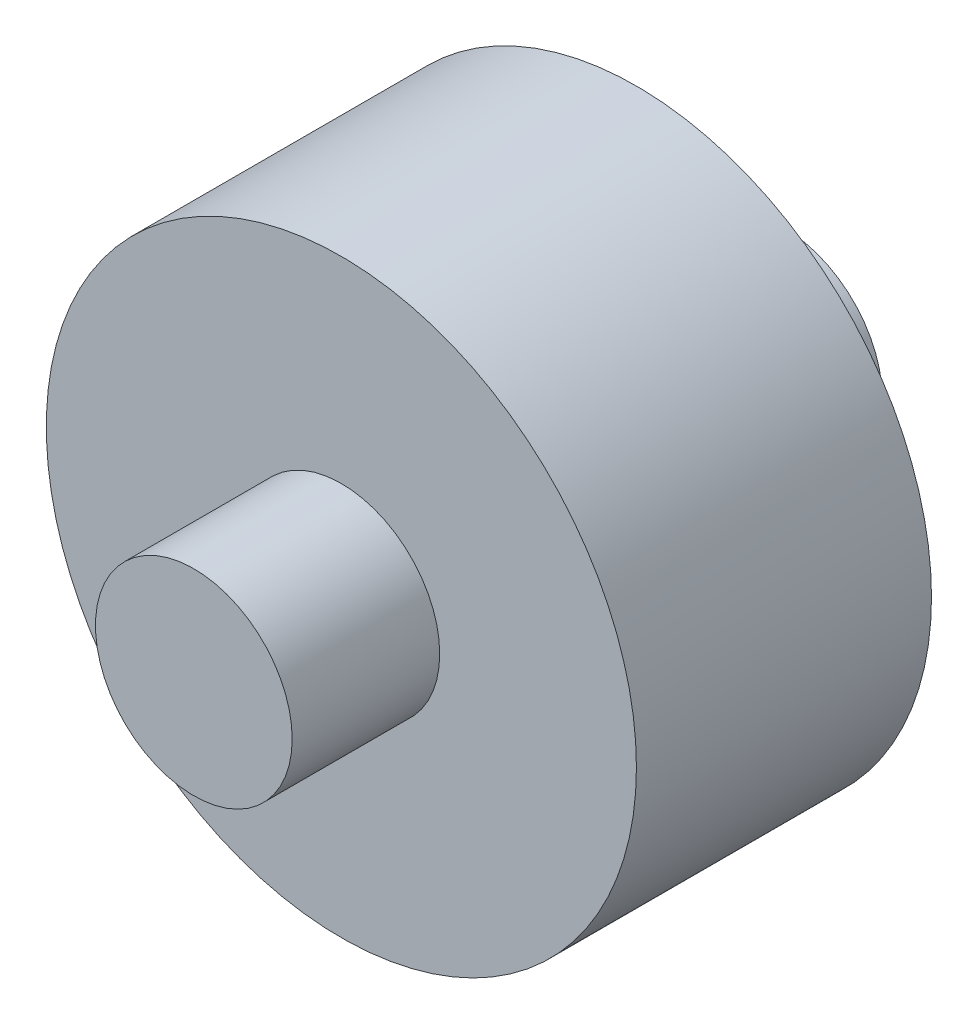
SolidWorks part; units mm, degrees
ref_plane "Front Plane" through (0, 0, 0) normal (0, 0, 1) x (1, 0, 0)
ref_plane "Top Plane" through (0, 0, 0) normal (0, 1, 0) x (1, 0, 0)
ref_plane "Right Plane" through (0, 0, 0) normal (1, 0, 0) x (0, 0, -1)
sketch "Sketch1" plane through (0, 0, 0) normal (0, 0, 1) x (1, 0, 0)
  circle A0 centre (0, 0) radius 9.525
  dimension "D1" = 19.05
extrude "Boss-Extrude1" add sketch "Sketch1" along normal mid plane 9.525
sketch "Sketch2" plane through (0, 0, 0) normal (0, 0, 1) x (1, 0, 0)
  circle A0 centre (0, 0) radius 3.175
  dimension "D1" = 6.35
extrude "Boss-Extrude2" add sketch "Sketch2" along normal mid plane 19.05
sketch "Sketch3" plane through (0, 0, 0) normal (1, 0, 0) x (0, 0, -1)
  circle A0 centre (0, 0) radius 3.175
  dimension "D1" = 6.35
extrude "Cut-Extrude1" cut sketch "Sketch3" against normal through all
